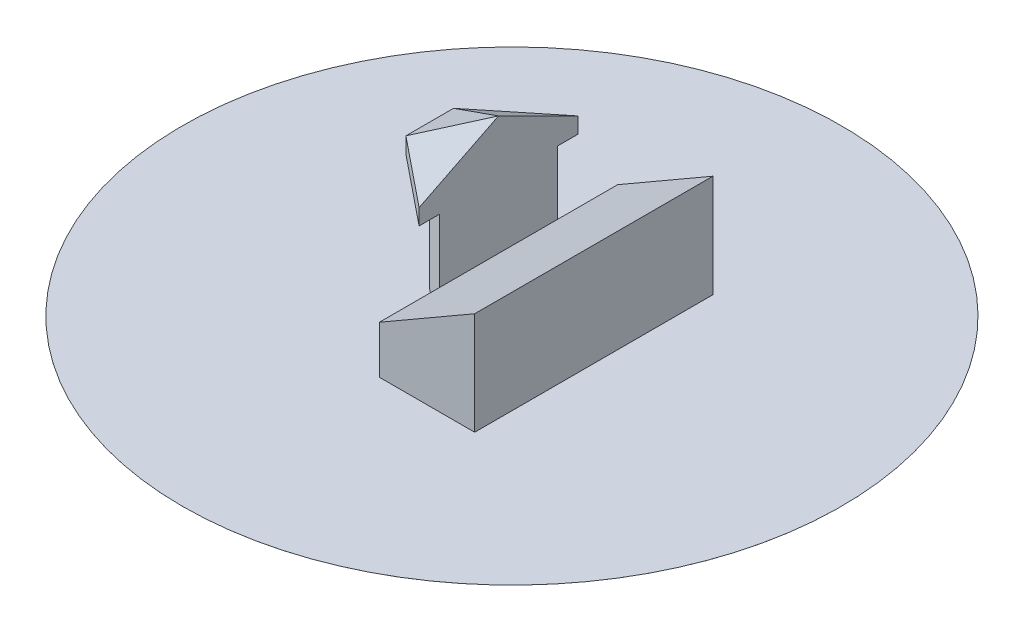
SolidWorks part; units mm, degrees
ref_plane "Front" through (0, 0, 0) normal (0, 0, 1) x (1, 0, 0)
ref_plane "Top" through (0, 0, 0) normal (0, 1, 0) x (1, 0, 0)
ref_plane "Right" through (0, 0, 0) normal (1, 0, 0) x (0, 0, -1)
sketch "Sketch1" plane through (0, 0, 0) normal (0, 0, 1) x (1, 0, 0)
  line L0 (0, 0) -> (0, 30)
  line L1 (0, 30) -> (60, 64.641)
  line L2 (60, 64.641) -> (60, 0)
  line L3 (60, 0) -> (0, 0)
  dimension "D1" = 60
  dimension "D2" = 30
  dimension "D3" = 30
extrude "Extrude1" add sketch "Sketch1" along normal mid plane 150
sketch "Sketch2" plane through (0, 0, 0) normal (0, 1, 0) x (1, 0, 0)
  line L0 (0, 50) -> (0, -50) construction
  line L1 (0, 37.1418) -> (-33.3013, 10.2247)
  line L2 (-33.3013, 10.2247) -> (-33.3013, -10.2247)
  line L3 (-33.3013, -10.2247) -> (0, -37.1418)
  line L4 (0, 50) -> (-43.3013, 15) construction
  line L5 (-43.3013, 15) -> (-43.3013, -15) construction
  line L6 (-43.3013, -15) -> (0, -50) construction
  line L7 (-33.3013, 15) -> (-33.3013, -15) construction
  line L8 (6.2862, 42.2229) -> (-37.0151, 7.2229) construction
  line L9 (-37.0151, -7.2229) -> (6.2862, -42.2229) construction
  line L10 (0, 37.1418) -> (0, -37.1418)
  dimension "D2" = 30
  dimension "D1" = 100
  dimension "D3" = 35
  dimension "D4" = 35
extrude "Extrude2" add sketch "Sketch2" along normal blind 70
sketch "Sketch3" plane through (0, 70, 0) normal (0, 1, 0) x (-1, 0, 0)
  line L0 (0, -50) -> (43.3013, -15)
  line L1 (43.3013, -15) -> (43.3013, 15)
  line L2 (43.3013, 15) -> (0, 50)
  line L3 (0, 50) -> (0, -50)
extrude "Extrude3" add sketch "Sketch3" along normal blind 10
sketch "Sketch4" plane through (0, 80, 0) normal (0, 1, 0) x (-1, 0, 0)
  line L0 (0, -50) -> (43.3013, -15)
  line L1 (43.3013, -15) -> (43.3013, 15)
  line L2 (43.3013, 15) -> (0, 50)
  line L3 (0, 50) -> (0, -50)
sketch "Sketch5" plane through (0, 0, 0) normal (0, 0, 1) x (1, 0, 0)
  line L0 (-43.3013, 80) -> (8.9052, 110.1414) construction
  line L1 (0, 80) -> (0, 111.9608) construction
  line L2 (0, 80) -> (-43.3013, 80) construction
  point P9 (0, 105)
  dimension "D1" = 30
loft "Loft1" add profiles "Sketch4", "Sketch5"
sketch "Sketch6" plane through (0, 0, 0) normal (0, 1, 0) x (1, 0, 0)
  line L0 (60, 75) -> (-43.3013, -74.781) construction
  circle A0 centre (8.3494, 0.1095) radius 207.5
  dimension "D1" = 415
extrude "Extrude4" add sketch "Sketch6" along normal blind 0.01
